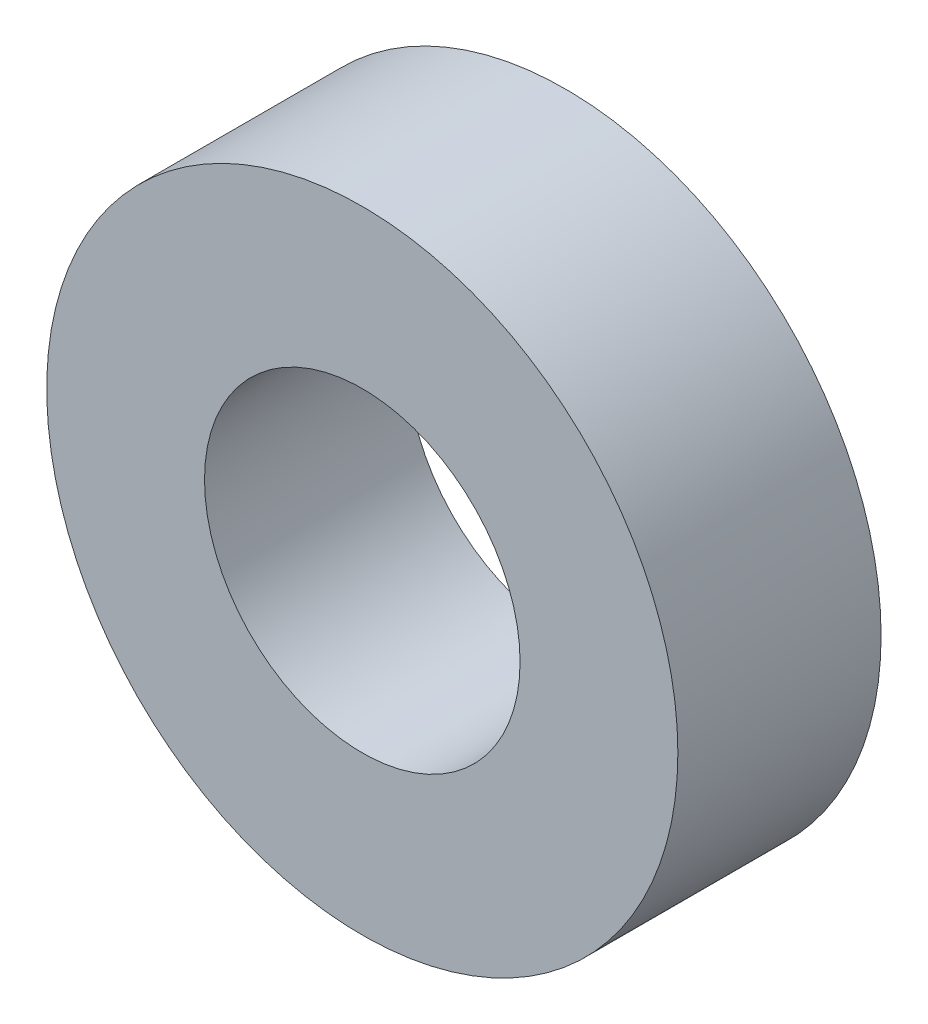
SolidWorks part; units mm, degrees
ref_plane "Front Plane" through (0, 0, 0) normal (0, 0, 1) x (1, 0, 0)
ref_plane "Top Plane" through (0, 0, 0) normal (0, 1, 0) x (1, 0, 0)
ref_plane "Right Plane" through (0, 0, 0) normal (1, 0, 0) x (0, 0, -1)
sketch "Sketch1" plane through (0, 0, 0) normal (0, 0, 1) x (1, 0, 0)
  circle A0 centre (0, 0) radius 4.7625
  circle A1 centre (0, 0) radius 9.525
  dimension "D1" = 9.525
  dimension "D2" = 19.05
extrude "Boss-Extrude1" add sketch "Sketch1" along normal blind 6.134
